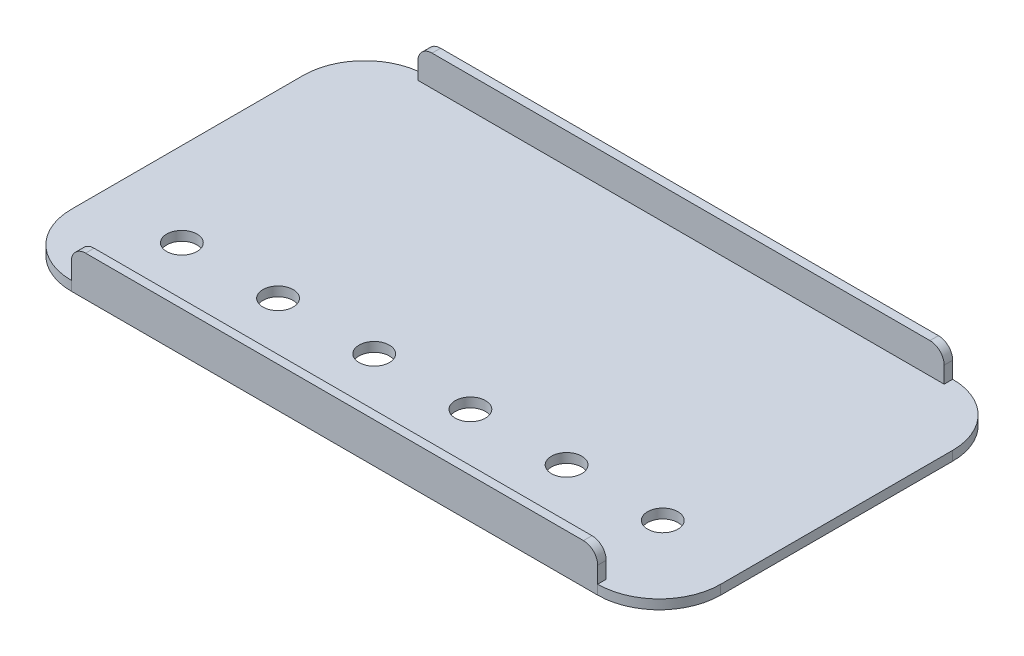
SolidWorks part; units mm, degrees
material "1060 Alloy"
ref_plane "Front Plane" through (0, 0, 0) normal (0, 0, 1) x (1, 0, 0)
ref_plane "Top Plane" through (0, 0, 0) normal (0, 1, 0) x (1, 0, 0)
ref_plane "Right Plane" through (0, 0, 0) normal (1, 0, 0) x (0, 0, -1)
sketch "Sketch1" plane through (0, 0, 0) normal (0, 1, 0) x (1, 0, 0)
  line L1 (27.8, -18.75) -> (-27.8, -18.75)
  line L2 (34.3, -12.25) -> (34.3, 12.25)
  line L3 (27.8, 18.75) -> (-27.8, 18.75)
  line L4 (-34.3, -12.25) -> (-34.3, 12.25)
  line L5 (34.3, -18.75) -> (-34.3, 18.75) construction
  line L6 (34.3, 18.75) -> (-34.3, -18.75) construction
  arc A0 (-27.8, 18.75) -> (-34.3, 12.25) centre (-27.8, 12.25) ccw
  arc A1 (34.3, 12.25) -> (27.8, 18.75) centre (27.8, 12.25) ccw
  arc A2 (27.8, -18.75) -> (34.3, -12.25) centre (27.8, -12.25) ccw
  arc A3 (-27.8, -18.75) -> (-34.3, -12.25) centre (-27.8, -12.25) cw
  point P0 (0, 0)
  dimension "D3" = 6.5
  dimension "D4" = 6.5
  dimension "D1" = 37.5
  dimension "D2" = 68.6
extrude "Boss-Extrude1" add sketch "Sketch1" along normal blind 1
sketch "Sketch2" plane through (0, 1, 0) normal (0, 1, 0) x (1, 0, 0)
  point P0 (-27.8, -18.75)
  point P1 (27.8, -18.75)
sketch "Sketch3" plane through (0, 1, 0) normal (0, 1, 0) x (1, 0, 0)
  line L0 (-34.3, 0) -> (34.3, 0) construction
  line L1 (-27.8, -18.75) -> (27.8, -18.75)
  line L2 (-27.8, -18.75) -> (-27.8, -17.85)
  line L3 (-27.8, -17.85) -> (27.8, -17.85)
  line L4 (27.8, -18.75) -> (27.8, -17.85)
  line L5 (-34.3, 12.25) -> (-34.3, -12.25) construction
  line L6 (34.3, -12.25) -> (34.3, 12.25) construction
  line L7 (27.8, 18.75) -> (27.8, 17.85)
  line L8 (-27.8, 18.75) -> (-27.8, 17.85)
  line L9 (-27.8, 18.75) -> (27.8, 18.75)
  line L10 (-27.8, 17.85) -> (27.8, 17.85)
  dimension "D1" = 0.9
  dimension "D2" = 55.6
extrude "Boss-Extrude2" add sketch "Sketch3" along normal blind 3.24
fillet "Fillet1" radius 1.5 1 edges at (-27.8, 4.24, 18.3)
fillet "Fillet2" radius 1.5 1 edges at (27.8, 4.24, 18.3)
fillet "Fillet3" radius 1.5 1 edges at (27.8, 4.24, -18.3)
fillet "Fillet4" radius 1.5 1 edges at (-27.8, 4.24, -18.3)
sketch "Sketch5" plane through (0, 1, 0) normal (0, 1, 0) x (1, 0, 0)
  line L2 (-34.3, 12.25) -> (-34.3, -12.25) construction
  line L3 (-26.3, -18.75) -> (26.3, -18.75) construction
  circle A11 centre (-25.4, -9.4746) radius 1.6
  circle A12 centre (-15.24, -9.4746) radius 1.6
  circle A13 centre (-5.08, -9.4746) radius 1.6
  circle A14 centre (5.08, -9.4746) radius 1.6
  circle A15 centre (15.24, -9.4746) radius 1.6
  circle A16 centre (25.4, -9.4746) radius 1.6
  dimension "D3" = 10.16
  dimension "D4" = 8.9
  dimension "D5" = 9.2754
  dimension "D2" = 3.2
  dimension "D1" = 6
extrude "Cut-Extrude2" cut sketch "Sketch5" against normal up to next
